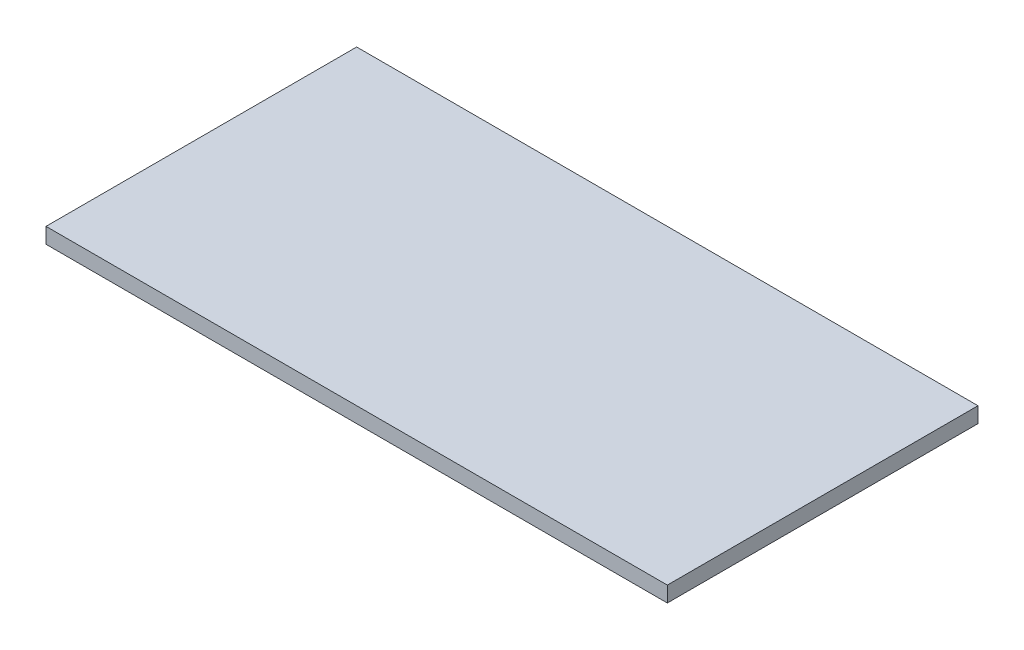
SolidWorks part; units mm, degrees
ref_plane "Front Plane" through (0, 0, 0) normal (0, 0, 1) x (1, 0, 0)
ref_plane "Top Plane" through (0, 0, 0) normal (0, 1, 0) x (1, 0, 0)
ref_plane "Right Plane" through (0, 0, 0) normal (1, 0, 0) x (0, 0, -1)
sketch "Sketch1" plane through (0, 0, 0) normal (0, 1, 0) x (1, 0, 0)
  line L1 (127, -63.5) -> (-127, -63.5)
  line L2 (127, -63.5) -> (127, 63.5)
  line L3 (127, 63.5) -> (-127, 63.5)
  line L4 (-127, -63.5) -> (-127, 63.5)
  line L5 (127, -63.5) -> (-127, 63.5) construction
  line L6 (127, 63.5) -> (-127, -63.5) construction
  point P0 (0, 0)
  dimension "D1" = 127
  dimension "D2" = 254
extrude "Boss-Extrude1" add sketch "Sketch1" along normal blind 6.35
sketch "Sketch2" plane through (0, 0, 0) normal (0, 1, 0) x (1, 0, 0)
  line L0 (-127, 0) -> (127, 0) construction
  line L1 (-127, 63.5) -> (-127, -63.5) construction
  line L2 (127, -63.5) -> (127, 63.5) construction
  line L3 (0, 63.5) -> (0, -63.5) construction
  line L4 (127, 63.5) -> (-127, 63.5) construction
  line L5 (-127, -63.5) -> (127, -63.5) construction
  line L6 (-107.95, -63.5) -> (-107.95, -57.15)
  line L7 (-127, -50.8) -> (-120.65, -50.8)
  line L8 (-9.398, -63.5) -> (-9.398, -57.15)
  line L9 (-127, 50.8) -> (-120.65, 50.8)
  line L10 (-120.65, -50.8) -> (-120.65, -57.15)
  line L11 (-120.65, -57.15) -> (-107.95, -57.15)
  line L12 (-107.95, 63.5) -> (-107.95, 57.15)
  line L13 (-120.65, 57.15) -> (-107.95, 57.15)
  line L14 (-120.65, 57.15) -> (-120.65, 50.8)
  line L15 (-9.398, 63.5) -> (-9.398, 57.15)
  line L16 (9.398, 63.5) -> (9.398, 57.15)
  line L17 (9.398, -63.5) -> (9.398, -57.15)
  line L18 (107.95, -63.5) -> (107.95, -57.15)
  line L19 (120.65, -57.15) -> (107.95, -57.15)
  line L20 (120.65, -50.8) -> (120.65, -57.15)
  line L21 (127, -50.8) -> (120.65, -50.8)
  line L22 (127, 50.8) -> (120.65, 50.8)
  line L23 (107.95, 63.5) -> (107.95, 57.15)
  line L24 (120.65, 57.15) -> (120.65, 50.8)
  line L25 (120.65, 57.15) -> (107.95, 57.15)
  line L26 (-9.398, -57.15) -> (9.398, -57.15)
  line L27 (-9.398, 57.15) -> (9.398, 57.15)
  dimension "D1" = 19.05
  dimension "D2" = 6.35
  dimension "D3" = 6.35
  dimension "D4" = 98.552
  dimension "D5" = 6.35
  dimension "D6" = 6.35
  dimension "D7" = 101.6
  dimension "D8" = 12.7
